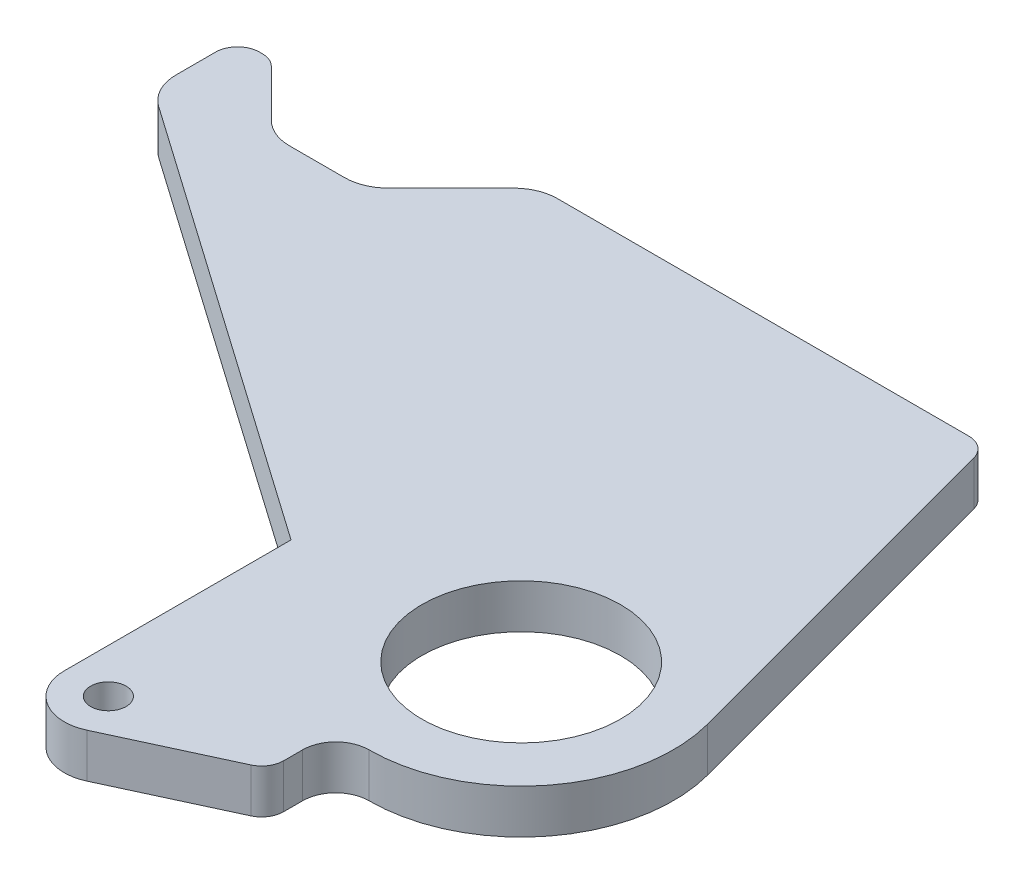
SolidWorks part; units mm, degrees
material "6061 Alloy"
ref_plane "Front Plane" through (0, 0, 0) normal (0, 0, 1) x (1, 0, 0)
ref_plane "Top Plane" through (0, 0, 0) normal (0, 1, 0) x (1, 0, 0)
ref_plane "Right Plane" through (0, 0, 0) normal (1, 0, 0) x (0, 0, -1)
sketch "Sketch1" plane through (0, 0, 0) normal (0, 1, 0) x (1, 0, 0)
  line L0 (4.08, 60.325) -> (-55.0879, 60.325)
  line L1 (-59.578, 58.4651) -> (-68.5582, 49.4849)
  line L2 (-73.0484, 47.625) -> (-80.9391, 47.625)
  line L3 (-85.4293, 49.4849) -> (-92.1645, 56.2201)
  line L4 (-94.4095, 57.15) -> (-94.7737, 57.15)
  line L5 (-97.9488, 53.975) -> (-97.9488, 48.2991)
  line L6 (-95.241, 43.0975) -> (-31.75, -1.3593)
  line L7 (-31.75, -1.3593) -> (-31.75, -33.9852)
  line L8 (-22.7333, -39.7481) -> (-6.6042, -32.2847)
  line L9 (-4.7625, -29.4032) -> (-4.7625, -26.67)
  line L10 (21.161, 5.6701) -> (7.1468, 57.9718)
  circle A0 centre (-25.4, -33.9852) radius 2.5527
  circle A1 centre (0, 0) radius 14.2875
  arc A2 (-55.0879, 60.325) -> (-59.578, 58.4651) centre (-55.0879, 53.975) ccw
  arc A3 (-68.5582, 49.4849) -> (-73.0484, 47.625) centre (-73.0484, 53.975) cw
  arc A4 (-80.9391, 47.625) -> (-85.4293, 49.4849) centre (-80.9391, 53.975) cw
  arc A5 (-92.1645, 56.2201) -> (-94.4095, 57.15) centre (-94.4095, 53.975) ccw
  arc A6 (-94.7737, 57.15) -> (-97.9488, 53.975) centre (-94.7737, 53.975) ccw
  arc A7 (-97.9488, 48.2991) -> (-95.241, 43.0975) centre (-91.5988, 48.2991) ccw
  arc A8 (-31.75, -33.9852) -> (-22.7333, -39.7481) centre (-25.4, -33.9852) ccw
  arc A9 (-6.6042, -32.2847) -> (-4.7625, -29.4032) centre (-7.9375, -29.4032) ccw
  arc A10 (-4.7625, -26.67) -> (0, -21.9075) centre (0, -26.67) cw
  arc A11 (0, -21.9075) -> (21.161, 5.6701) centre (0, 0) ccw
  arc A12 (7.1468, 57.9718) -> (4.08, 60.325) centre (4.08, 57.15) ccw
  point P35 (0, 0)
  dimension "D1" = 5.1054
  dimension "D2" = 28.575
  dimension "D3" = 6.35
  dimension "D4" = 6.35
  dimension "D5" = 3.175
  dimension "D6" = 2.7078
  dimension "D7" = 3.5392
  dimension "D8" = 6.35
  dimension "D9" = 6.35
  dimension "D10" = 3.175
  dimension "D11" = 4.7625
  dimension "D12" = 21.9075
  dimension "D13" = 5.7843
  dimension "D14" = 24.9004
  dimension "D15" = 66.1988
  dimension "D16" = 75.2154
  dimension "D17" = 90.0113
  dimension "D18" = 102.0288
  dimension "D19" = 105.0956
  dimension "D20" = 12.0259
  dimension "D21" = 89.7282
extrude "Boss-Extrude1" add sketch "Sketch1" against normal blind 6.35
